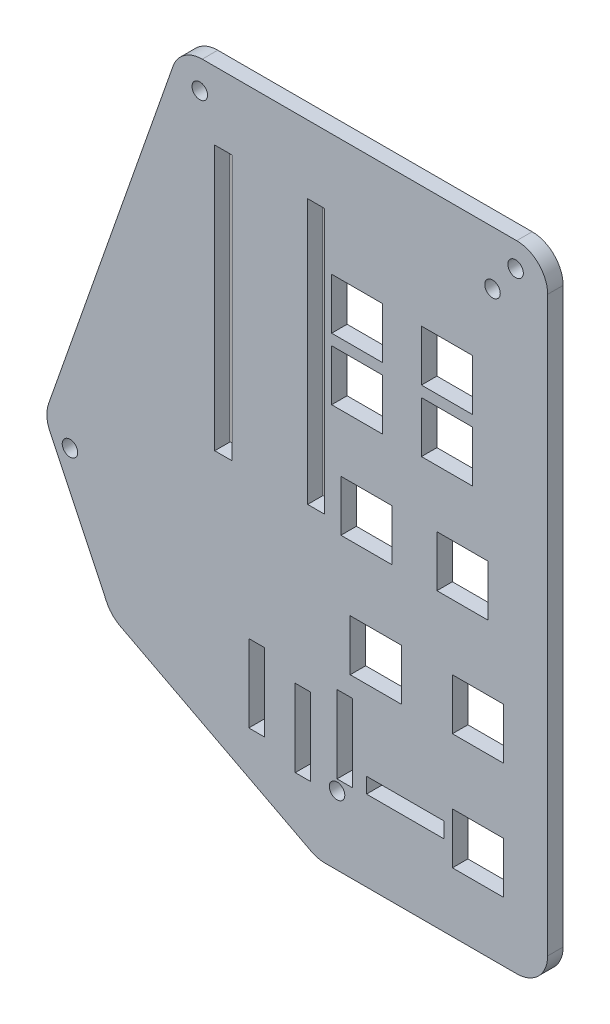
SolidWorks part; units mm, degrees
ref_plane "Front Plane" through (0, 0, 0) normal (0, 0, 1) x (1, 0, 0)
ref_plane "Top Plane" through (0, 0, 0) normal (0, 1, 0) x (1, 0, 0)
ref_plane "Right Plane" through (0, 0, 0) normal (1, 0, 0) x (0, 0, -1)
sketch "Sketch1" plane through (0, 0, 0) normal (0, 0, 1) x (1, 0, 0)
  line L6 (-20.066, -57.15) -> (46.99, -57.15) construction
  line L7 (-12.446, -73.152) -> (46.99, -73.152) construction
  line L8 (-3.3141, 6.35) -> (48.26, 6.35)
  line L9 (53.34, 1.27) -> (53.34, -92.71)
  line L10 (48.26, -97.79) -> (16.847, -97.79)
  line L16 (-8.1072, 2.9529) -> (-28.5162, -55.1739)
  line L18 (-20.066, -57.15) -> (-29.21, -57.15) construction
  line L26 (0, 0) -> (46.99, 0) construction
  line L27 (46.99, 0) -> (46.99, -88.9) construction
  line L28 (46.99, -88.9) -> (17.78, -88.9) construction
  line L29 (17.78, -88.9) -> (-12.446, -73.152) construction
  line L30 (-12.446, -73.152) -> (-20.066, -57.15) construction
  line L31 (-20.066, -57.15) -> (0, 0) construction
  line L32 (46.99, -57.15) -> (46.99, -88.9) construction
  line L33 (17.78, -88.9) -> (15.603, -97.79) construction
  line L34 (-12.446, -73.152) -> (-17.9301, -78.4424) construction
  line L35 (14.4997, -97.2152) -> (-16.7505, -80.9336)
  line L36 (-28.3096, -59.0409) -> (-18.9898, -78.6124)
  arc A0 (14.4997, -97.2152) -> (16.847, -97.79) centre (16.847, -92.71) ccw
  arc A1 (-28.5162, -55.1739) -> (-28.3096, -59.0409) centre (-23.723, -56.8568) ccw
  arc A2 (-16.7505, -80.9336) -> (-18.9898, -78.6124) centre (-14.4033, -76.4284) cw
  arc A3 (53.34, -92.71) -> (48.26, -97.79) centre (48.26, -92.71) cw
  arc A4 (48.26, 6.35) -> (53.34, 1.27) centre (48.26, 1.27) cw
  arc A5 (-8.1072, 2.9529) -> (-3.3141, 6.35) centre (-3.3141, 1.27) cw
  circle A6 centre (48.0822, 2.286) radius 1.27
  circle A7 centre (-3.7187, 1.651) radius 1.27
  circle A8 centre (-25.0123, -59.762) radius 1.27
  point P25 (53.34, -97.79)
  point P28 (53.34, 6.35)
  dimension "D11" = 5.2578
  dimension "D8" = 5.08
  dimension "D9" = 2.54
  dimension "D1" = 88.9
  dimension "D2" = 29.21
  dimension "D3" = 59.436
  dimension "D4" = 67.056
  dimension "D5" = 104.14
  dimension "D6" = 82.55
  dimension "D7" = 46.99
  dimension "D10" = 4.064
  dimension "D12" = 4.699
  dimension "D13" = 103.76
  dimension "D14" = 4.572
  dimension "D15" = 4.826
  dimension "D16" = 2.667
  dimension "D17" = 108.51
extrude "Boss-Extrude1" add sketch "Sketch1" along normal blind 2.54
sketch "Sketch3" plane through (0, 0, 2.54) normal (0, 0, 1) x (1, 0, 0)
  line L0 (46.99, -88.9) -> (0, -88.9) construction
  line L6 (-20.066, -57.15) -> (46.99, -57.15) construction
  line L7 (-12.446, -73.152) -> (46.99, -73.152) construction
  line L8 (0, 0) -> (46.99, 0) construction
  line L9 (46.99, 0) -> (46.99, -88.9) construction
  line L10 (46.99, -88.9) -> (17.78, -88.9) construction
  line L11 (17.78, -88.9) -> (-12.446, -73.152) construction
  line L12 (-12.446, -73.152) -> (-20.066, -57.15) construction
  line L13 (-20.066, -57.15) -> (0, 0) construction
sketch "Sketch5" plane through (0, 0, 0) normal (0, 0, -1) x (-1, 0, 0)
  line L0 (-46.99, 0) -> (-46.99, -17.78) construction
  line L1 (-46.99, 0) -> (-1.524, 0) construction
  line L2 (-46.99, -17.78) -> (-36.83, -17.78) construction
  line L3 (-46.99, 0) -> (-46.99, -27.94) construction
  line L8 (-41.021, -13.589) -> (-32.639, -13.589)
  line L9 (-41.021, -13.589) -> (-41.021, -21.971)
  line L10 (-46.99, 0) -> (-46.99, -45.72) construction
  line L15 (-41.021, -21.971) -> (-32.639, -21.971)
  line L16 (-32.639, -13.589) -> (-32.639, -21.971)
  line L17 (-46.99, 0) -> (-46.99, -88.9) construction
  line L18 (-46.99, -45.72) -> (-39.37, -45.72) construction
  line L19 (-41.021, -13.589) -> (-32.639, -21.971) construction
  line L20 (-46.99, 0) -> (-46.99, -64.77) construction
  line L21 (-43.561, -41.529) -> (-35.179, -41.529)
  line L22 (-43.561, -41.529) -> (-43.561, -49.911)
  line L23 (-43.561, -49.911) -> (-35.179, -49.911)
  line L24 (-35.179, -41.529) -> (-35.179, -49.911)
  line L25 (-43.561, -41.529) -> (-35.179, -49.911) construction
  line L26 (-43.561, -49.911) -> (-35.179, -41.529) construction
  line L27 (-46.99, -64.77) -> (-41.91, -64.77) construction
  line L28 (-41.021, -21.971) -> (-32.639, -13.589) construction
  line L29 (-46.99, -27.94) -> (-36.83, -27.94) construction
  line L30 (-46.99, 0) -> (-46.99, -83.82) construction
  line L31 (-41.021, -23.749) -> (-32.639, -23.749)
  line L32 (-41.021, -23.749) -> (-41.021, -32.131)
  line L33 (-41.021, -32.131) -> (-32.639, -32.131)
  line L34 (-32.639, -23.749) -> (-32.639, -32.131)
  line L35 (-41.021, -23.749) -> (-32.639, -32.131) construction
  line L36 (-41.021, -32.131) -> (-32.639, -23.749) construction
  line L37 (-46.101, -60.579) -> (-37.719, -60.579)
  line L38 (-46.101, -60.579) -> (-46.101, -68.961)
  line L39 (-46.101, -68.961) -> (-37.719, -68.961)
  line L40 (-37.719, -60.579) -> (-37.719, -68.961)
  line L41 (-46.101, -60.579) -> (-37.719, -68.961) construction
  line L42 (-46.101, -68.961) -> (-37.719, -60.579) construction
  line L43 (-46.99, -83.82) -> (-41.91, -83.82) construction
  line L44 (-36.83, -17.78) -> (-22.098, -17.78) construction
  line L45 (-46.101, -79.629) -> (-37.719, -79.629)
  line L46 (-46.101, -79.629) -> (-46.101, -88.011)
  line L47 (-46.101, -88.011) -> (-37.719, -88.011)
  line L48 (-37.719, -79.629) -> (-37.719, -88.011)
  line L49 (-46.101, -79.629) -> (-37.719, -88.011) construction
  line L50 (-46.101, -88.011) -> (-37.719, -79.629) construction
  line L51 (-36.83, -27.94) -> (-22.098, -27.94) construction
  line L52 (-39.37, -45.72) -> (-23.622, -45.72) construction
  line L53 (-41.91, -64.77) -> (-25.146, -64.77) construction
  line L54 (-46.99, 0) -> (-16.764, 0) construction
  line L55 (-26.289, -13.589) -> (-17.907, -13.589)
  line L56 (-26.289, -13.589) -> (-26.289, -21.971)
  line L57 (-26.289, -21.971) -> (-17.907, -21.971)
  line L58 (-17.907, -13.589) -> (-17.907, -21.971)
  line L59 (-26.289, -13.589) -> (-17.907, -21.971) construction
  line L60 (-26.289, -21.971) -> (-17.907, -13.589) construction
  line L61 (-26.289, -23.749) -> (-17.907, -23.749)
  line L62 (-26.289, -23.749) -> (-26.289, -32.131)
  line L63 (-26.289, -32.131) -> (-17.907, -32.131)
  line L64 (-17.907, -23.749) -> (-17.907, -32.131)
  line L65 (-26.289, -23.749) -> (-17.907, -32.131) construction
  line L66 (-26.289, -32.131) -> (-17.907, -23.749) construction
  line L67 (-27.813, -41.529) -> (-19.431, -41.529)
  line L68 (-27.813, -41.529) -> (-27.813, -49.911)
  line L69 (-27.813, -49.911) -> (-19.431, -49.911)
  line L70 (-19.431, -41.529) -> (-19.431, -49.911)
  line L71 (-27.813, -41.529) -> (-19.431, -49.911) construction
  line L72 (-27.813, -49.911) -> (-19.431, -41.529) construction
  line L73 (-29.337, -60.579) -> (-20.955, -60.579)
  line L74 (-29.337, -60.579) -> (-29.337, -68.961)
  line L75 (-29.337, -68.961) -> (-20.955, -68.961)
  line L76 (-20.955, -60.579) -> (-20.955, -68.961)
  line L77 (-29.337, -60.579) -> (-20.955, -68.961) construction
  line L78 (-29.337, -68.961) -> (-20.955, -60.579) construction
  line L79 (0, 0) -> (-46.99, 0) construction
  line L80 (-16.764, 0) -> (-16.764, -4.826) construction
  line L81 (-46.99, 0) -> (-13.97, 0) construction
  line L82 (-13.97, 0) -> (-13.97, -4.826) construction
  line L83 (-1.524, 0) -> (-1.524, -4.826) construction
  line L84 (-46.99, 0) -> (-17.1256, 0) construction
  line L85 (-1.524, 0) -> (-1.524, -48.26) construction
  line L86 (-46.99, 0) -> (1.27, 0) construction
  line L87 (1.27, 0) -> (1.27, -4.826) construction
  line L88 (-16.764, 0) -> (-16.764, -48.26) construction
  line L90 (-16.764, -4.826) -> (-13.97, -4.826)
  line L91 (-16.764, -4.826) -> (-16.764, -48.26)
  line L92 (-16.764, -48.26) -> (-13.97, -48.26)
  line L93 (-13.97, -4.826) -> (-13.97, -48.26)
  line L94 (-1.524, -4.826) -> (1.27, -4.826)
  line L95 (-1.524, -4.826) -> (-1.524, -48.26)
  line L96 (-1.524, -48.26) -> (1.27, -48.26)
  line L97 (1.27, -4.826) -> (1.27, -48.26)
  dimension "D2" = 8.382
  dimension "D3" = 64.77
  dimension "D4" = 8.382
  dimension "D5" = 10.16
  dimension "D6" = 17.78
  dimension "D7" = 8.382
  dimension "D8" = 8.382
  dimension "D9" = 45.72
  dimension "D10" = 7.62
  dimension "D11" = 8.382
  dimension "D12" = 8.382
  dimension "D13" = 27.94
  dimension "D14" = 10.16
  dimension "D15" = 5.08
  dimension "D16" = 8.382
  dimension "D17" = 8.382
  dimension "D18" = 8.382
  dimension "D19" = 8.382
  dimension "D20" = 83.82
  dimension "D21" = 5.08
  dimension "D22" = 8.382
  dimension "D23" = 8.382
  dimension "D24" = 14.732
  dimension "D25" = 8.382
  dimension "D26" = 8.382
  dimension "D27" = 14.732
  dimension "D28" = 8.382
  dimension "D29" = 8.382
  dimension "D30" = 15.748
  dimension "D31" = 8.382
  dimension "D32" = 8.382
  dimension "D33" = 16.764
  dimension "D34" = 30.226
  dimension "D35" = 4.826
  dimension "D36" = 33.02
  dimension "D37" = 4.826
  dimension "D38" = 45.466
  dimension "D39" = 4.826
  dimension "D40" = 48.26
  dimension "D41" = 4.826
  dimension "D42" = 48.26
  dimension "D43" = 48.26
extrude "Cut-Extrude1" cut sketch "Sketch5" against normal through all
sketch "Sketch7" plane through (0, 0, 2.54) normal (0, 0, 1) x (1, 0, 0)
  line L0 (46.99, 0) -> (44.2976, 0) construction
  line L1 (0, 0) -> (46.99, 0) construction
  line L2 (44.2976, 0) -> (44.2976, -2.4892) construction
  line L3 (46.99, 0) -> (1.6002, 0) construction
  line L4 (1.6002, 0) -> (1.6002, -2.4384) construction
  line L5 (-20.066, -57.15) -> (-17.4498, -57.15) construction
  line L6 (-20.066, -57.15) -> (46.99, -57.15) construction
  line L7 (-12.446, -73.152) -> (-10.5918, -73.152) construction
  line L8 (-12.446, -73.152) -> (46.99, -73.152) construction
  line L9 (-10.5918, -73.152) -> (-10.5918, -71.3486) construction
  line L10 (17.78, -88.9) -> (17.78, -86.5378) construction
  line L11 (17.78, -86.5378) -> (18.796, -86.5378) construction
  circle A0 centre (44.2976, -2.4892) radius 1.27
  circle A4 centre (18.796, -86.5378) radius 1.27
  dimension "D3" = 2.54
  dimension "D14" = 2.54
  dimension "D1" = 2.6924
  dimension "D2" = 2.4892
  dimension "D4" = 45.3898
  dimension "D5" = 2.4384
  dimension "D7" = 2.6162
  dimension "D9" = 1.8542
  dimension "D10" = 1.8034
  dimension "D12" = 2.3622
  dimension "D13" = 1.016
extrude "Cut-Extrude3" cut sketch "Sketch7" against normal through all
sketch "Sketch8" plane through (0, 0, 2.54) normal (0, 0, 1) x (1, 0, 0)
  line L0 (23.622, -82.042) -> (36.322, -82.042)
  line L1 (23.622, -82.042) -> (23.622, -84.582)
  line L2 (23.622, -84.582) -> (36.322, -84.582)
  line L3 (36.322, -82.042) -> (36.322, -84.582)
  line L4 (18.796, -72.136) -> (21.336, -72.136)
  line L5 (18.796, -72.136) -> (18.796, -84.836)
  line L6 (18.796, -84.836) -> (21.336, -84.836)
  line L7 (21.336, -72.136) -> (21.336, -84.836)
  line L8 (11.938, -74.676) -> (14.478, -74.676)
  line L9 (11.938, -74.676) -> (11.938, -87.376)
  line L10 (11.938, -87.376) -> (14.478, -87.376)
  line L11 (14.478, -74.676) -> (14.478, -87.376)
  line L12 (4.318, -72.136) -> (6.858, -72.136)
  line L13 (4.318, -72.136) -> (4.318, -84.836)
  line L14 (4.318, -84.836) -> (6.858, -84.836)
  line L15 (6.858, -72.136) -> (6.858, -84.836)
  line L16 (46.99, -83.312) -> (36.322, -83.312) construction
  line L17 (46.99, 0) -> (46.99, -88.9) construction
  line L18 (36.322, -83.312) -> (36.322, 0) construction
  line L19 (0, 0) -> (46.99, 0) construction
  line L20 (21.336, -72.136) -> (46.99, -72.136) construction
  line L21 (21.336, -72.136) -> (21.336, 0) construction
  line L22 (6.858, -72.136) -> (46.99, -72.136) construction
  line L23 (14.478, -74.676) -> (46.99, -74.676) construction
  line L24 (14.478, -74.676) -> (14.478, 0) construction
  line L25 (6.858, -72.136) -> (6.858, 0) construction
  dimension "D1" = 12.7
  dimension "D2" = 2.54
  dimension "D3" = 12.7
  dimension "D4" = 2.54
  dimension "D5" = 12.7
  dimension "D6" = 2.54
  dimension "D7" = 12.7
  dimension "D8" = 2.54
  dimension "D9" = 10.668
  dimension "D10" = 83.312
  dimension "D11" = 25.654
  dimension "D12" = 72.136
  dimension "D13" = 32.512
  dimension "D14" = 74.676
  dimension "D15" = 40.132
  dimension "D16" = 72.136
extrude "Cut-Extrude4" cut sketch "Sketch8" against normal through all
